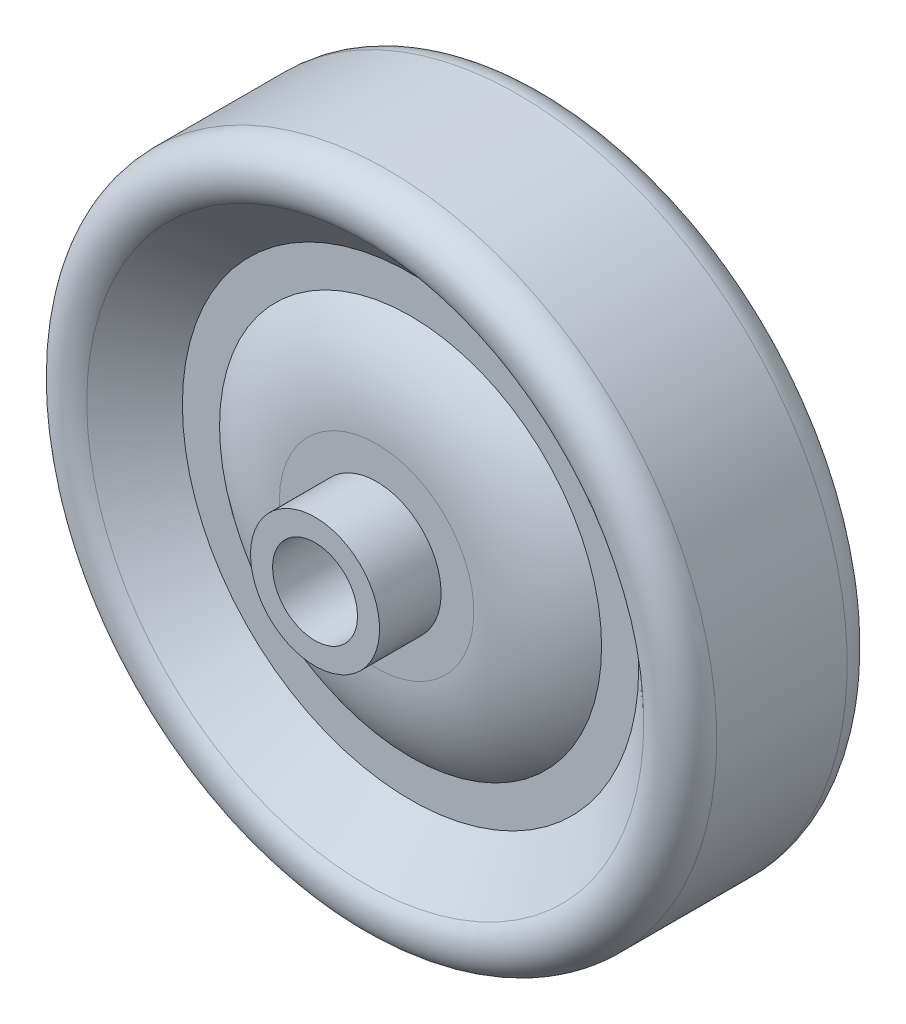
SolidWorks part; units mm, degrees
ref_plane "Front" through (0, 0, 0) normal (0, 0, 1) x (1, 0, 0)
ref_plane "Top" through (0, 0, 0) normal (0, 1, 0) x (1, 0, 0)
ref_plane "Right" through (0, 0, 0) normal (1, 0, 0) x (0, 0, -1)
sketch "Sketch1" plane through (0, 0, 0) normal (1, 0, 0) x (0, 0, -1)
  line L0 (0, 24.6062) -> (4.8816, 24.6062)
  line L1 (0, 24.6062) -> (0, 3.175)
  line L2 (0, 3.175) -> (10.3188, 3.175)
  line L3 (10.3188, 3.175) -> (10.3187, 4.826)
  line L4 (10.3187, 4.826) -> (5.715, 4.826)
  line L5 (10.3187, 4.826) -> (10.3188, -4.826) construction
  line L6 (10.3188, 3.175) -> (10.3188, -3.175) construction
  line L7 (6.5632, 20.8309) -> (3.175, 17.0656)
  line L8 (0, 24.6062) -> (0, -24.6062) construction
  line L9 (10.3187, 0) -> (-10.3187, 0) construction
  line L10 (7.1437, 22.3441) -> (-7.1438, 22.3441) construction
  line L11 (5.715, 7.2695) -> (5.715, 4.826)
  line L12 (3.175, 14.2875) -> (3.175, 17.0656)
  line L19 (5.715, 4.826) -> (-5.715, 4.826) construction
  line L20 (3.175, 15.6766) -> (-3.175, 15.6766) construction
  arc A0 (4.8816, 24.6062) -> (6.5632, 20.8309) centre (4.8816, 22.3441) cw
  arc A2 (3.175, 14.2875) -> (5.715, 7.2695) centre (-5.2505, 7.2695) cw
  point P19 (0, 22.3441)
  point P27 (0, 4.826)
  point P31 (0, 15.6766)
  dimension "D2" = 2.2622
  dimension "D1" = 9.652
  dimension "D3" = 11.43
  dimension "D4" = 6.35
  dimension "D5" = 14.2875
  dimension "D6" = 2.7781
  dimension "D7" = 2.4435
revolve "Revolve1" add sketch "Sketch1" angle 360 mid plane about L9
mirror "Mirror1" about plane through (0, 0, 0) normal (0, 0, 1) of bodies 109
equation "\"D1@Sketch1\" = \"Bore Dia@Sketch1\" * 1.52"
